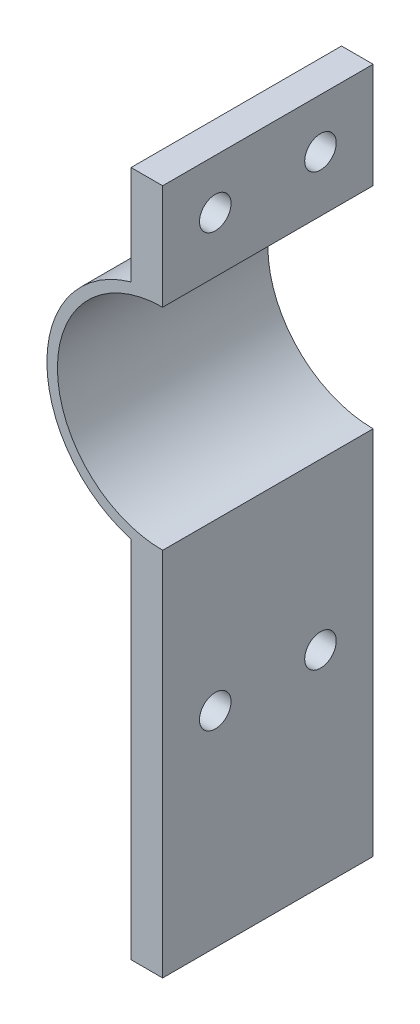
SolidWorks part; units mm, degrees
ref_plane "前视基准面" through (0, 0, 0) normal (0, 0, 1) x (1, 0, 0)
ref_plane "上视基准面" through (0, 0, 0) normal (0, 1, 0) x (1, 0, 0)
ref_plane "右视基准面" through (0, 0, 0) normal (1, 0, 0) x (0, 0, -1)
sketch "草图1" plane through (0, 0, 0) normal (0, 0, 1) x (1, 0, 0)
  line L0 (0, -45.2) -> (-3, -45.2)
  line L1 (0, 10) -> (0, 20)
  line L2 (0, -45.2) -> (0, -10)
  line L3 (-3, -45.2) -> (-3, -10.583)
  line L4 (0, 20) -> (-3, 20)
  line L5 (-3, 20) -> (-3, 10.583)
  arc A0 (0, 10) -> (0, -10) centre (0, 0) ccw
  arc A1 (-3, 10.583) -> (-3, -10.583) centre (0, 0) ccw
extrude "凸台-拉伸1" add sketch "草图1" along normal blind 20 contours L5 A1 L3 L0 L2 A0 L1 L4
ref_plane "基准面1" through (-3, 0, 0) normal (-1, 0, 0) x (0, 0, 1)
sketch "草图2" plane through (-3, 0, 0) normal (-1, 0, 0) x (0, 0, 1)
  circle A0 centre (5, 15.2915) radius 1.5
  circle A1 centre (15, 15.2915) radius 1.5
  circle A2 centre (5, -25.7) radius 1.5
  circle A3 centre (15, -25.7) radius 1.5
extrude "切除-拉伸1" cut sketch "草图2" against normal blind 20
